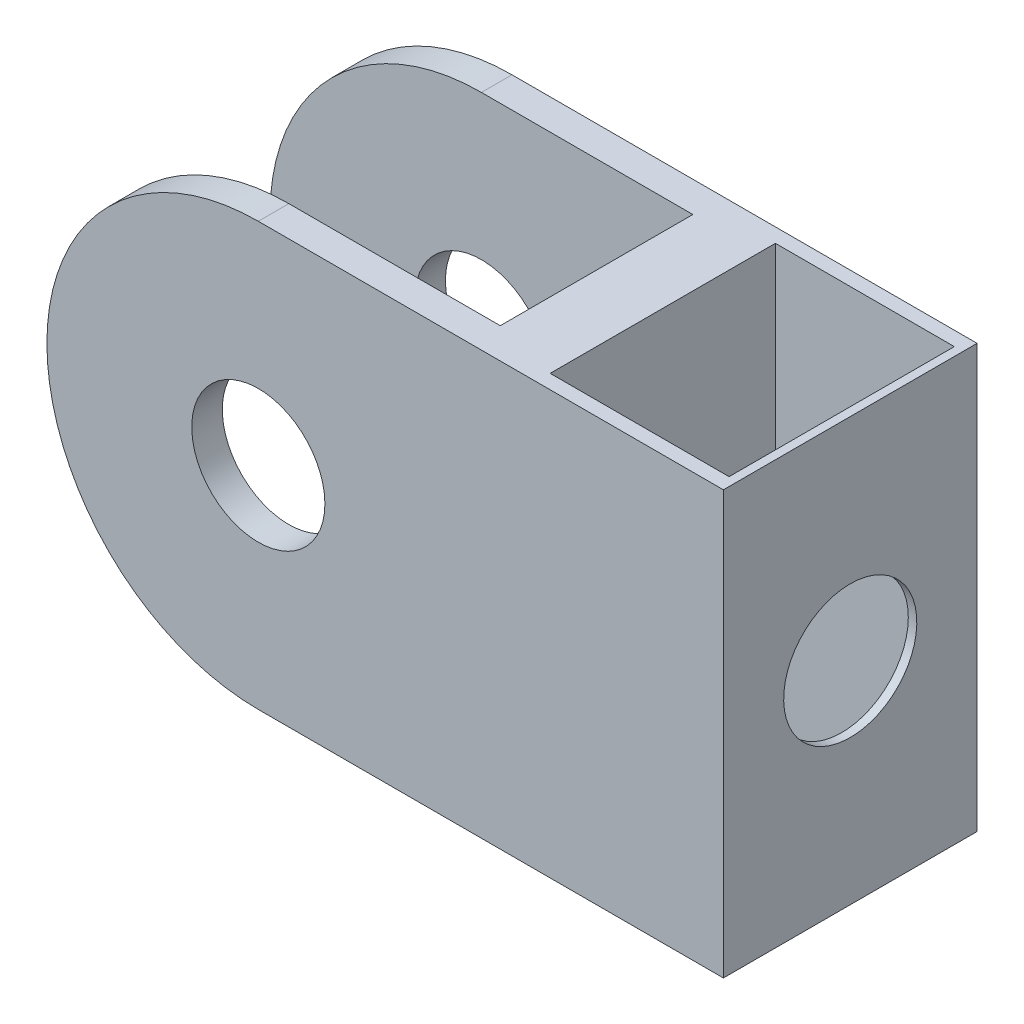
SolidWorks part; units mm, degrees
ref_plane "Front Plane" through (0, 0, 0) normal (0, 0, 1) x (1, 0, 0)
ref_plane "Top Plane" through (0, 0, 0) normal (0, 1, 0) x (1, 0, 0)
ref_plane "Right Plane" through (0, 0, 0) normal (1, 0, 0) x (0, 0, -1)
sketch "Sketch1" plane through (0, 0, 0) normal (0, 0, 1) x (1, 0, 0)
  line L1 (0, 12.7) -> (27.94, 12.7)
  line L3 (0, -12.7) -> (27.94, -12.7)
  line L4 (27.94, 12.7) -> (27.94, -12.7)
  arc A0 (0, 12.7) -> (0, -12.7) centre (0, 0) ccw
  circle A1 centre (0, 0) radius 4
  dimension "D1" = 12.7
  dimension "D3" = 8
  dimension "D2" = 27.94
  dimension "D4" = 25.4
extrude "Boss-Extrude1" add sketch "Sketch1" along normal blind 15.24
sketch "Sketch2" plane through (0, 12.7, 0) normal (0, 1, 0) x (1, 0, 0)
  line L0 (-12.7, 0) -> (-12.7, -15.24) construction
  line L1 (-12.7, -1.8352) -> (12.7, -1.8352)
  line L2 (-12.7, -1.8352) -> (-12.7, -13.4049)
  line L3 (-12.7, -13.4049) -> (12.7, -13.4049)
  line L4 (12.7, -1.8352) -> (12.7, -13.4049)
  line L5 (-12.7, 0) -> (-12.7, -1.8352) construction
  line L6 (-12.7, -15.24) -> (-12.7, -13.4049) construction
  dimension "D1" = 11.5697
  dimension "D2" = 25.4
extrude "Cut-Extrude1" cut sketch "Sketch2" against normal through all
sketch "Sketch3" plane through (0, 12.7, 0) normal (0, 1, 0) x (1, 0, 0)
  line L0 (22.053, -0.8545) -> (22.053, 0) construction
  line L1 (16.678, -14.3855) -> (27.4281, -14.3855)
  line L2 (16.678, -14.3855) -> (16.678, -0.8545)
  line L3 (16.678, -0.8545) -> (27.4281, -0.8545)
  line L4 (27.4281, -14.3855) -> (27.4281, -0.8545)
  line L5 (16.678, -14.3855) -> (27.4281, -0.8545) construction
  line L6 (16.678, -0.8545) -> (27.4281, -14.3855) construction
  line L7 (27.94, 0) -> (0, 0) construction
  line L8 (22.053, -14.3855) -> (22.053, -15.24) construction
  line L9 (27.94, -15.24) -> (0, -15.24) construction
  line L12 (16.3191, 0) -> (16.3191, -15.24) construction
  point P0 (22.053, -7.62)
  point P13 (16.3191, -7.62)
extrude "Cut-Extrude2" cut sketch "Sketch3" against normal through all
sketch "Sketch4" plane through (27.94, 0, 0) normal (1, 0, 0) x (0, 0, -1)
  line L0 (-15.24, -12.7) -> (-15.24, 12.7) construction
  line L1 (-15.24, 12.7) -> (0, 12.7) construction
  circle A0 centre (-7.62, 0) radius 4
  dimension "D1" = 8
  dimension "D2" = 7.62
  dimension "D3" = 12.7
extrude "Cut-Extrude3" cut sketch "Sketch4" against normal through all
